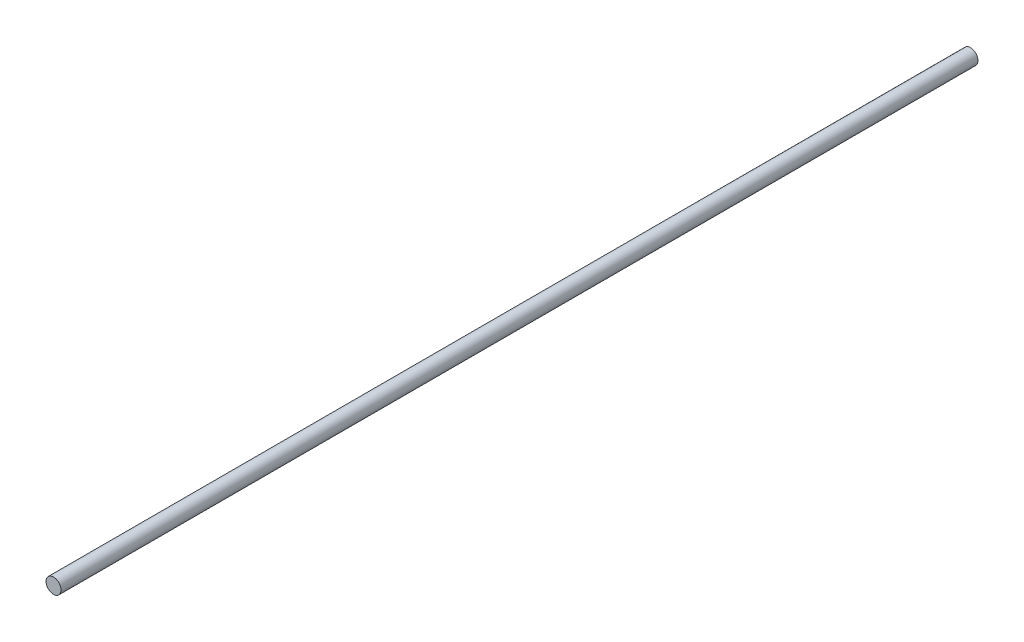
SolidWorks part; units mm, degrees
ref_plane "Plan de face" through (0, 0, 0) normal (0, 0, 1) x (1, 0, 0)
ref_plane "Plan de dessus" through (0, 0, 0) normal (0, 1, 0) x (1, 0, 0)
ref_plane "Plan de droite" through (0, 0, 0) normal (1, 0, 0) x (0, 0, -1)
sketch "Esquisse1" plane through (0, 0, 0) normal (0, 0, 1) x (1, 0, 0)
  circle A0 centre (0, 0) radius 4
  dimension "D1" = 8
extrude "Boss.-Extru.1" add sketch "Esquisse1" along normal blind 488
